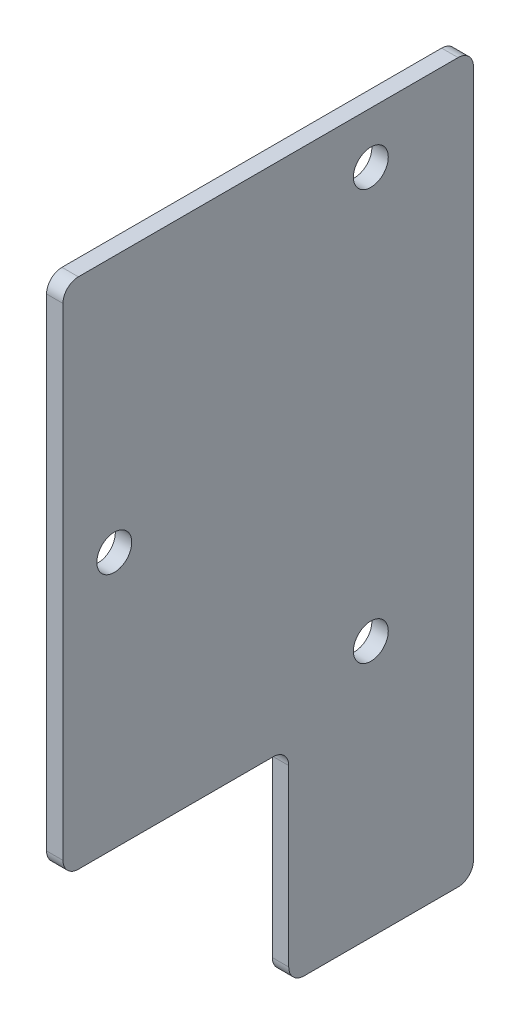
SolidWorks part; units mm, degrees
material "E-Glass Fiber"
ref_plane "Front Plane" through (0, 0, 0) normal (0, 0, 1) x (1, 0, 0)
ref_plane "Top Plane" through (0, 0, 0) normal (0, 1, 0) x (1, 0, 0)
ref_plane "Right Plane" through (0, 0, 0) normal (1, 0, 0) x (0, 0, -1)
sketch "Sketch1" plane through (0, 0, 0) normal (1, 0, 0) x (0, 0, -1)
  line L1 (-20, 25) -> (20, 25)
  line L2 (-20, 25) -> (-20, -25)
  line L3 (-20, -25) -> (20, -25) construction
  line L4 (20, 25) -> (20, -25)
  line L5 (-20, 25) -> (20, -25) construction
  line L6 (-20, -25) -> (20, 25) construction
  line L14 (20, -45) -> (20, -25)
  line L15 (-20, -25) -> (2, -25)
  line L16 (2, -25) -> (2, -45)
  line L17 (2, -45) -> (20, -45)
  point P0 (0, 0)
  point P9 (0, 0)
  dimension "D1" = 50
  dimension "D2" = 40
  dimension "D3" = 18
  dimension "D4" = 20
extrude "Boss-Extrude1" add sketch "Sketch1" along normal blind 1.6002
sketch "Sketch2" plane through (1.6002, 0, 0) normal (1, 0, 0) x (0, 0, -1)
  line L1 (10, 20) -> (-15, 20) construction
  line L2 (10, 20) -> (10, -20) construction
  line L3 (10, -20) -> (-15, -20) construction
  line L4 (-15, 20) -> (-15, -20) construction
  line L5 (10, 20) -> (-15, -20) construction
  line L6 (10, -20) -> (-15, 20) construction
  line L8 (-20, 25) -> (-20, -25) construction
  point P0 (-2.5, 0)
  point P6 (0, 0)
  point P9 (0, -4.1215)
  dimension "D1" = 40
  dimension "D2" = 25
  dimension "D3" = 5
hole_wizard "M3 Clearance Hole1" positions "Sketch3" profile "Sketch4" hole size "M3" standard "ANSI Metric"
sketch "Sketch3" plane through (1.6002, 0, 0) normal (1, 0, 0) x (0, 0, -1)
  line L0 (-15, 20) -> (-15, -20) construction
  point P3 (10, 20)
  point P6 (10, -20)
  point P13 (-15, 0)
sketch "Sketch4" plane through (1.6002, 20, -10) normal (0, 1, 0) x (0, 0, -1)
  line L0 (0, 0) -> (0, 7.0215)
  line L1 (0, 7.0215) -> (1.7, 6)
  line L2 (1.7, 6) -> (1.7, 0)
  line L5 (1.7, 0) -> (0, 0)
  line L10 (0, 7.0215) -> (-1.7, 6) construction
  line L11 (0, -6.35) -> (0, 107.95) construction
  dimension "Hole Dia." = 3.4
  dimension "Hole Depth" = 6
  dimension "Drill Angle" = 118
sketch "Sketch5" plane through (1.6002, 0, 0) normal (-1, 0, 0) x (0, 0, 1)
  line L0 (15, 5.391) -> (15, 18) construction
  line L1 (13, 20) -> (-4.609, 20) construction
  line L3 (-10, 14.609) -> (-10, -14.609) construction
  line L5 (-4.609, -20) -> (13, -20) construction
  line L6 (15, -18) -> (15, -5.391) construction
  line L7 (14.5, 5.391) -> (14.5, 18)
  line L8 (13, 19.5) -> (-4.609, 19.5)
  line L9 (-9.5, 14.609) -> (-9.5, -14.609)
  line L10 (-4.609, -19.5) -> (13, -19.5)
  line L11 (14.5, -18) -> (14.5, -5.391)
  arc A0 (13.6957, 3.5158) -> (13.6957, -3.5158) centre (15, 0) ccw construction
  arc A1 (-8.6957, -16.4842) -> (-10, -14.609) centre (-8, -14.609) cw construction
  arc A2 (-6.4842, -18.6957) -> (-4.609, -20) centre (-4.609, -18) ccw construction
  arc A9 (-6.4842, 18.6957) -> (-8.6957, 16.4842) centre (-10, 20) cw construction
  arc A10 (-8.6957, -16.4842) -> (-6.4842, -18.6957) centre (-10, -20) cw construction
  arc A11 (13, -20) -> (15, -18) centre (13, -18) ccw construction
  arc A12 (13.6957, -3.5158) -> (15, -5.391) centre (13, -5.391) cw construction
  arc A13 (13.6957, 3.5158) -> (15, 5.391) centre (13, 5.391) ccw construction
  arc A14 (15, 18) -> (13, 20) centre (13, 18) ccw construction
  arc A15 (-6.4842, 18.6957) -> (-4.609, 20) centre (-4.609, 18) cw construction
  arc A16 (-8.6957, 16.4842) -> (-10, 14.609) centre (-8, 14.609) ccw construction
  arc A17 (14.5, 18) -> (13, 19.5) centre (13, 18) ccw
  arc A18 (-6.0154, 18.5217) -> (-4.609, 19.5) centre (-4.609, 18) cw
  arc A19 (-6.0154, 18.5217) -> (-8.5217, 16.0154) centre (-10, 20) cw
  arc A20 (-8.5217, 16.0154) -> (-9.5, 14.609) centre (-8, 14.609) ccw
  arc A21 (-8.5217, -16.0154) -> (-9.5, -14.609) centre (-8, -14.609) cw
  arc A22 (-8.5217, -16.0154) -> (-6.0154, -18.5217) centre (-10, -20) cw
  arc A23 (-6.0154, -18.5217) -> (-4.609, -19.5) centre (-4.609, -18) ccw
  arc A24 (13, -19.5) -> (14.5, -18) centre (13, -18) ccw
  arc A25 (13.5217, -3.9846) -> (14.5, -5.391) centre (13, -5.391) cw
  arc A26 (13.5217, 3.9846) -> (13.5217, -3.9846) centre (15, 0) ccw
  arc A27 (13.5217, 3.9846) -> (14.5, 5.391) centre (13, 5.391) ccw
  point P10 (-7.3483, 17.3483)
  point P12 (0, 0)
  point P13 (0, 0)
  point P14 (0, 0)
  point P15 (0, 0)
  point P18 (-10, -16.25)
  point P21 (-6.25, -20)
  point P26 (15, -3.75)
  point P33 (-6.25, 20)
  dimension "D2" = 2
  dimension "D1" = 3.75
  dimension "D3" = 0.5
extrude "Boss-Extrude2" [suppressed] add sketch "Sketch5" against normal blind 2
fillet "Fillet1" radius 1.5 6 edges at (0.8001, 25, -20) (0.8001, 25, 20) (0.8001, -45, -20) (0.8001, -45, -2) (0.8001, -25, -2) (0.8001, -25, 20)
